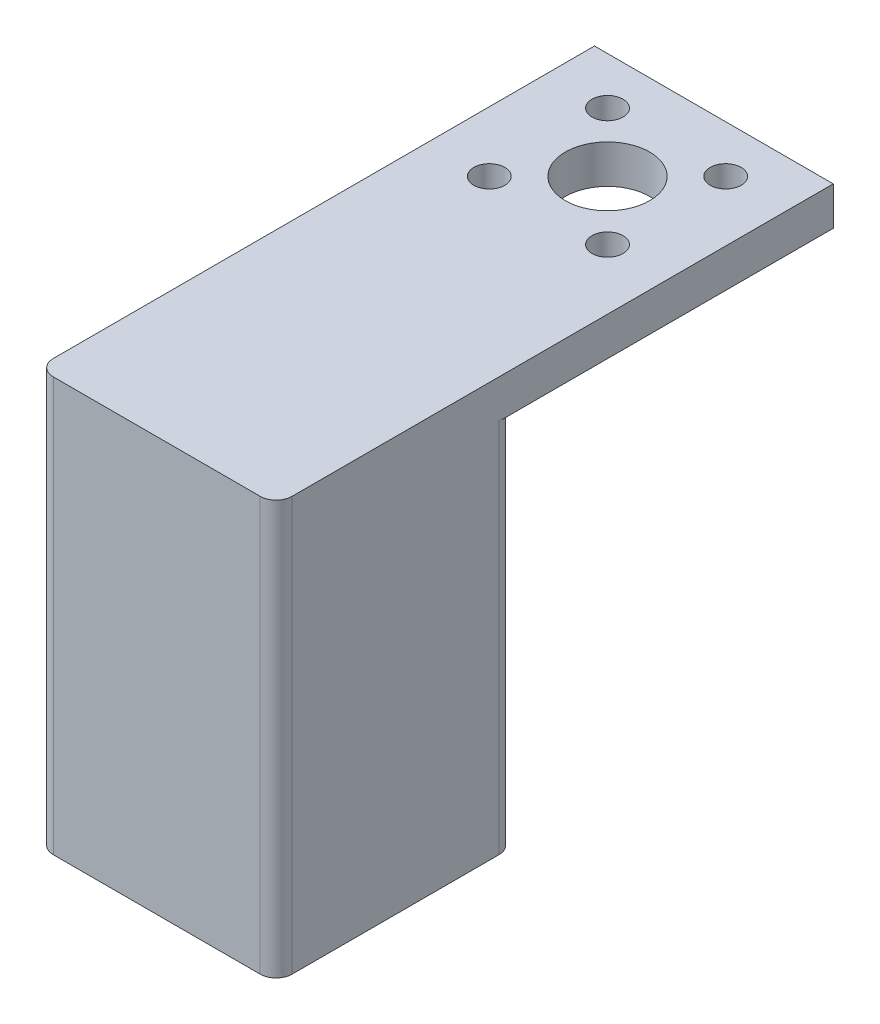
SolidWorks part; units mm, degrees
ref_plane "Alzado" through (0, 0, 0) normal (0, 0, 1) x (1, 0, 0)
ref_plane "Planta" through (0, 0, 0) normal (0, 1, 0) x (1, 0, 0)
ref_plane "Vista lateral" through (0, 0, 0) normal (1, 0, 0) x (0, 0, -1)
sketch "Croquis1" plane through (0, 0, 0) normal (0, 1, 0) x (1, 0, 0)
  line L1 (-15, 15) -> (15, 15)
  line L2 (-15, 15) -> (-15, -15)
  line L3 (-15, -15) -> (15, -15)
  line L4 (15, 15) -> (15, -15)
  line L5 (-15, 15) -> (15, -15) construction
  line L6 (-15, -15) -> (15, 15) construction
  line L7 (-12, 12) -> (12, 12)
  line L8 (-12, 12) -> (-12, -12)
  line L9 (-12, -12) -> (12, -12)
  line L10 (12, 12) -> (12, -12)
  line L11 (-12, 12) -> (12, -12) construction
  line L12 (-12, -12) -> (12, 12) construction
  point P0 (0, 0)
  point P6 (0, 0)
  dimension "D1" = 30
  dimension "D2" = 3
extrude "Saliente-Extruir1" add sketch "Croquis1" along normal blind 50
sketch "Croquis2" plane through (0, 50, 0) normal (0, 1, 0) x (1, 0, 0)
  line L1 (-15, 15) -> (15, 15)
  line L2 (-15, 15) -> (-15, -15)
  line L3 (-15, -15) -> (15, -15)
  line L4 (15, 15) -> (15, -15)
extrude "Saliente-Extruir2" add sketch "Croquis2" along normal blind 2
sketch "Croquis6" plane through (0, 0, -15) normal (0, 0, -1) x (-1, 0, 0)
  line L0 (-15, 52) -> (-15, 0) construction
  line L1 (15, 52) -> (-15, 52)
  line L2 (15, 52) -> (15, 47.1624)
  line L3 (15, 47.1624) -> (-15, 47.1624)
  line L4 (-15, 52) -> (-15, 47.1624)
extrude "Saliente-Extruir4" add sketch "Croquis6" along normal blind 40
sketch "Croquis7" plane through (0, 52, 0) normal (0, 1, 0) x (1, 0, 0)
  line L0 (0, 41.6346) -> (10.5, 41.6346) construction
  line L1 (0, 41.6346) -> (7.4246, 49.0592) construction
  line L2 (0, 55) -> (0, 22.7161) construction
  line L3 (-15, 55) -> (15, 55) construction
  circle A0 centre (0, 41.6346) radius 5.3
  circle A1 centre (0, 41.6346) radius 10.5 construction
  circle A2 centre (7.4246, 49.0592) radius 1.95
  circle A3 centre (7.4246, 34.21) radius 1.95
  circle A4 centre (-7.4246, 34.21) radius 1.95
  circle A5 centre (-7.4246, 49.0592) radius 1.95
  point P15 (0, 41.6346)
  dimension "D1" = 10.6
  dimension "D2" = 21
  dimension "D3" = 3.9
  dimension "D4" = 45
  dimension "D5" = 4
extrude "Cortar-Extruir2" cut sketch "Croquis7" against normal blind 40
fillet "Redondeo1" radius 2 8 edges at (-15, 26, 15) (15, 26, 15) (-12, 25, 12) (-12, 25, -12) (12, 25, 12) (12, 25, -12)
